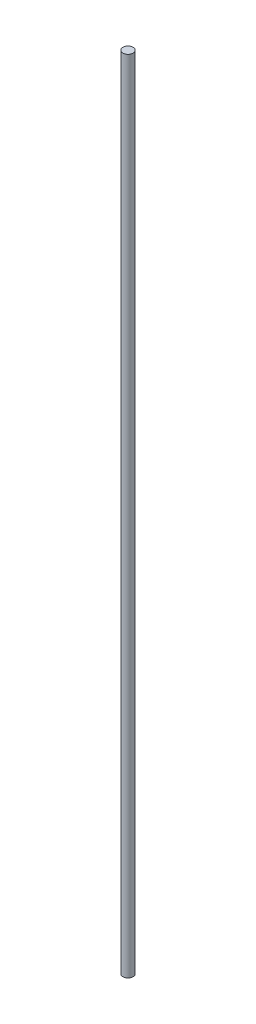
SolidWorks part; units mm, degrees
ref_plane "Front Plane" through (0, 0, 0) normal (0, 0, 1) x (1, 0, 0)
ref_plane "Top Plane" through (0, 0, 0) normal (0, 1, 0) x (1, 0, 0)
ref_plane "Right Plane" through (0, 0, 0) normal (1, 0, 0) x (0, 0, -1)
sketch "Sketch1" plane through (0, 0, 0) normal (0, 1, 0) x (1, 0, 0)
  circle A0 centre (0, 0) radius 20
  dimension "D1" = 40
extrude "Boss-Extrude1" add sketch "Sketch1" along normal blind 3131.82
sketch3d "3DSketch1" plane through (0, 0, 0) normal (0, 0, 1) x (1, 0, 0)
  dimension "D1" = 355.6
